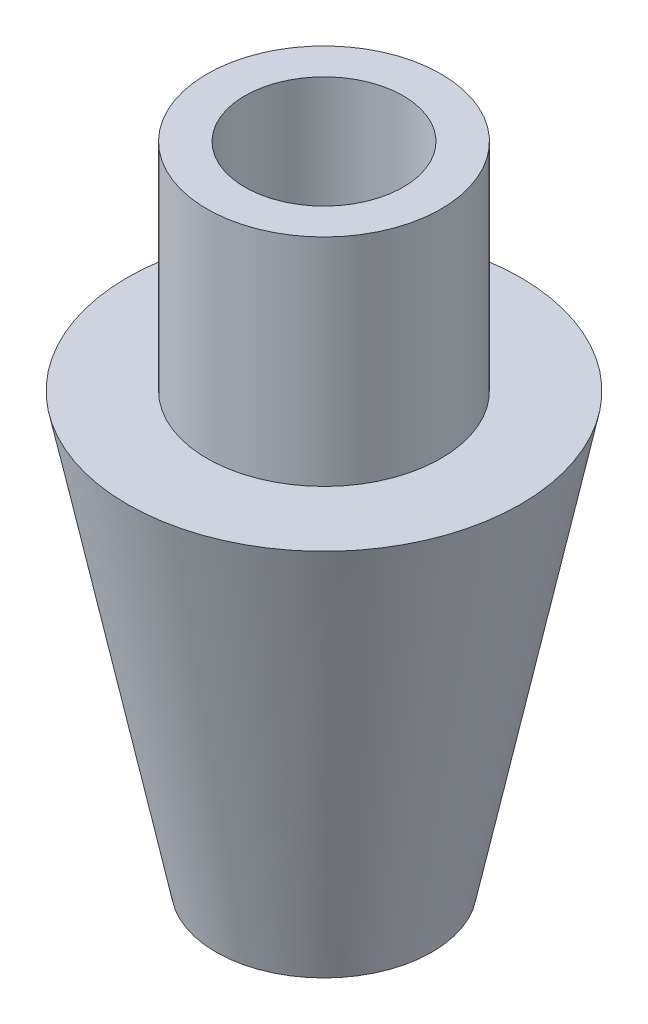
SolidWorks part; units mm, degrees
material "Nylon 6/10"
ref_plane "Front Plane" through (0, 0, 0) normal (0, 0, 1) x (1, 0, 0)
ref_plane "Top Plane" through (0, 0, 0) normal (0, 1, 0) x (1, 0, 0)
ref_plane "Right Plane" through (0, 0, 0) normal (1, 0, 0) x (0, 0, -1)
sketch "Sketch1" plane through (0, 0, 0) normal (1, 0, 0) x (0, 0, -1)
  line L0 (0, 0) -> (0, 52.8332) construction
  line L1 (-13.716, 0) -> (-19.05, 0)
  line L2 (-19.05, 0) -> (-34.6583, 76.2)
  line L3 (-34.6583, 76.2) -> (-20.6375, 76.2)
  line L4 (-20.6375, 76.2) -> (-20.6375, 114.3)
  line L5 (-20.6375, 114.3) -> (-13.97, 114.3)
  line L6 (-13.97, 114.3) -> (-13.97, 76.2)
  line L7 (-13.97, 76.2) -> (-13.716, 76.2)
  line L8 (-13.716, 76.2) -> (-13.716, 0)
  dimension "D1" = 13.716
  dimension "D2" = 19.05
  dimension "D3" = 34.6583
  dimension "D4" = 76.2
  dimension "D5" = 114.3
  dimension "D6" = 38.1
  dimension "D7" = 20.6375
  dimension "D8" = 13.97
revolve "Revolve1" add sketch "Sketch1" angle 360 about L0
